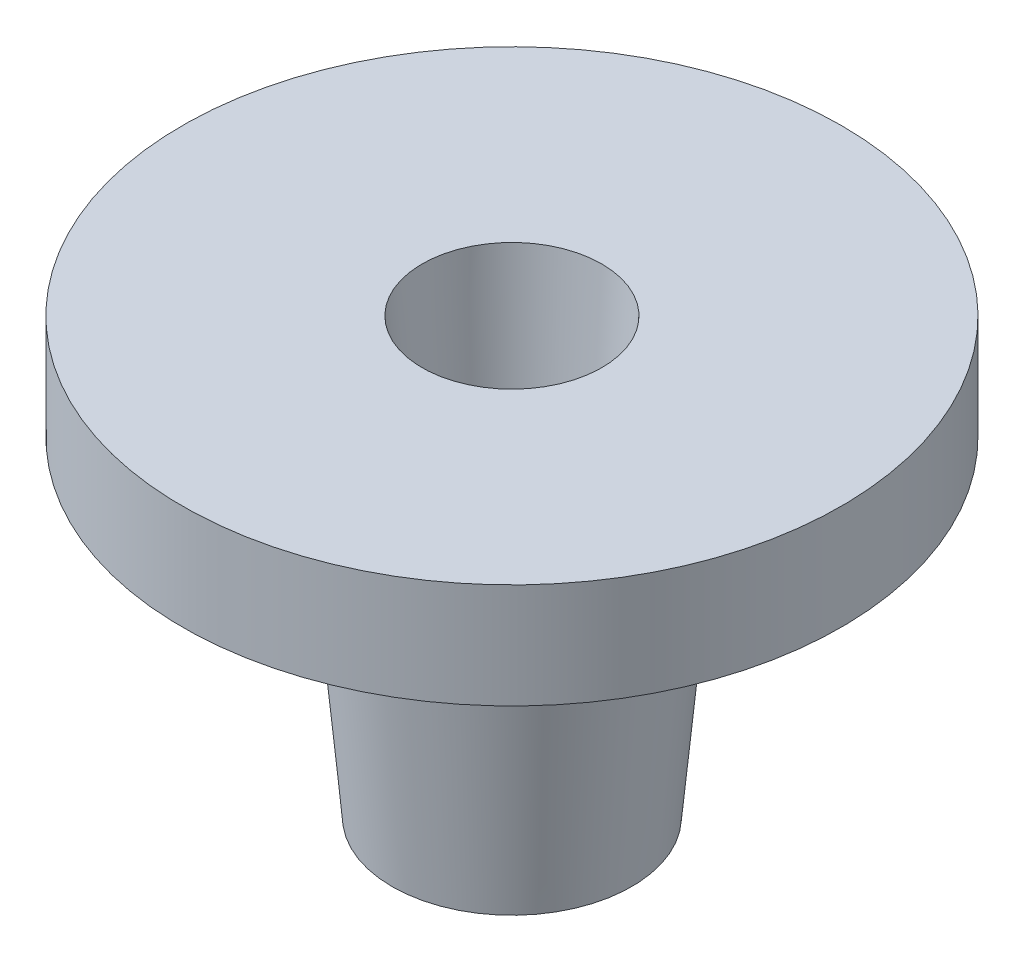
SolidWorks part; units mm, degrees
ref_plane "Front Plane" through (0, 0, 0) normal (0, 0, 1) x (1, 0, 0)
ref_plane "Top Plane" through (0, 0, 0) normal (0, 1, 0) x (1, 0, 0)
ref_plane "Right Plane" through (0, 0, 0) normal (1, 0, 0) x (0, 0, -1)
sketch "Sketch1" plane through (0, 0, 0) normal (0, 0, 1) x (1, 0, 0)
  line L0 (0, 0) -> (0, 11)
  line L1 (0, 11) -> (2, 11)
  line L2 (2, 11) -> (3, 0)
  line L3 (3, 0) -> (0, 0)
  line L4 (7, 0) -> (7, 10.6522) construction
  line L5 (0, 11) -> (-4, 11)
  line L6 (-4, 11) -> (-4, 14.5)
  line L7 (-4, 14.5) -> (4, 14.5)
  line L8 (3, 0) -> (5, 0)
  line L10 (5, 0) -> (4, 14.5)
  dimension "D1" = 7
  dimension "D2" = 2
  dimension "D3" = 3
  dimension "D4" = 11
  dimension "D5" = 3.5
  dimension "D6" = 4
  dimension "D7" = 2
  dimension "D8" = 2
revolve "Revolve1" add sketch "Sketch1" angle 360 about L4
